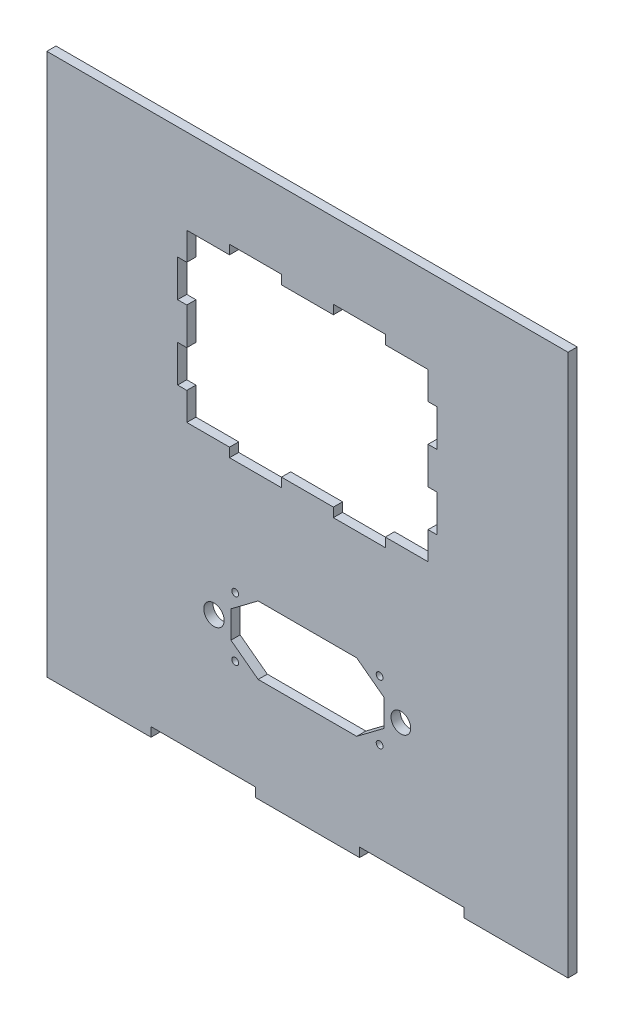
SolidWorks part; units mm, degrees
ref_plane "Ön Düzlem" through (0, 0, 0) normal (0, 0, 1) x (1, 0, 0)
ref_plane "Üst Düzlem" through (0, 0, 0) normal (0, 1, 0) x (1, 0, 0)
ref_plane "Sağ Düzlem" through (0, 0, 0) normal (1, 0, 0) x (0, 0, -1)
sketch "Sketch1" plane through (0, 0, 0) normal (0, 0, 1) x (1, 0, 0)
  line L21 (-46.02, -28) -> (-46.02, -25.3)
  line L22 (-15.34, -28) -> (-15.34, -25.3)
  line L23 (15.34, -28) -> (15.34, -25.3)
  line L24 (46.02, -28) -> (46.02, -25.3)
  line L26 (-76.7, -23) -> (-76.7, 13)
  line L27 (-76.7, -23) -> (-76.7, -25.3)
  line L28 (76.7, -23) -> (76.7, 13)
  line L30 (76.7, -25.3) -> (76.7, -23)
  line L33 (-46.02, -28) -> (-76.7, -28)
  line L34 (-76.7, -28) -> (-76.7, -25.3)
  line L35 (-15.34, -25.3) -> (-46.02, -25.3)
  line L36 (-15.34, -28) -> (15.34, -28)
  line L37 (15.34, -25.3) -> (46.02, -25.3)
  line L38 (46.02, -28) -> (76.7, -28)
  line L39 (76.7, -28) -> (76.7, -25.3)
  line L56 (-22.5, 16.5) -> (-14.5, 22.5)
  line L57 (-14.5, 22.5) -> (14.5, 22.5)
  line L58 (0, 2.5) -> (14.5, 2.5)
  line L59 (-14.5, 2.5) -> (-22.5, 8.5)
  line L60 (-22.5, 8.5) -> (-22.5, 16.5)
  line L61 (14.5, 2.5) -> (22.5, 8.5)
  line L62 (14.5, 22.5) -> (22.5, 16.5)
  line L63 (0, 2.5) -> (-14.5, 2.5)
  line L64 (22.5, 16.5) -> (22.5, 8.5)
  line L65 (35.5, 57.5) -> (22.92, 57.5)
  line L66 (35.5, 57.5) -> (35.5, 65.68)
  line L67 (35.5, 106.5) -> (22.92, 106.5)
  line L68 (-35.5, 57.5) -> (-35.5, 65.68)
  line L80 (76.7, 13) -> (76.7, 131.5)
  line L81 (-76.7, 131.5) -> (-76.7, 13)
  line L82 (76.7, 131.5) -> (-76.7, 131.5)
  line L84 (-22.92, 54.8) -> (-7.64, 54.8)
  line L85 (-22.92, 109.2) -> (-7.64, 109.2)
  line L88 (38.2, 65.68) -> (38.2, 76.56)
  line L89 (7.64, 109.2) -> (22.92, 109.2)
  line L91 (-38.2, 65.68) -> (-38.2, 76.56)
  line L93 (-38.2, 87.44) -> (-38.2, 98.32)
  line L95 (-38.2, 98.32) -> (-35.5, 98.32)
  line L96 (-38.2, 87.44) -> (-35.5, 87.44)
  line L97 (-38.2, 76.56) -> (-35.5, 76.56)
  line L98 (-38.2, 65.68) -> (-35.5, 65.68)
  line L99 (35.5, 65.68) -> (38.2, 65.68)
  line L100 (35.5, 76.56) -> (38.2, 76.56)
  line L101 (35.5, 87.44) -> (38.2, 87.44)
  line L102 (35.5, 98.32) -> (38.2, 98.32)
  line L103 (-22.92, 109.2) -> (-22.92, 106.5)
  line L104 (-7.64, 109.2) -> (-7.64, 106.5)
  line L105 (7.64, 109.2) -> (7.64, 106.5)
  line L106 (22.92, 109.2) -> (22.92, 106.5)
  line L107 (-22.92, 57.5) -> (-22.92, 54.8)
  line L108 (-7.64, 57.5) -> (-7.64, 54.8)
  line L109 (7.64, 57.5) -> (7.64, 54.8)
  line L110 (22.92, 57.5) -> (22.92, 54.8)
  line L111 (-22.92, 106.5) -> (-35.5, 106.5)
  line L112 (7.64, 106.5) -> (-7.64, 106.5)
  line L113 (35.5, 98.32) -> (35.5, 106.5)
  line L114 (35.5, 76.56) -> (35.5, 87.44)
  line L115 (7.64, 57.5) -> (-7.64, 57.5)
  line L116 (-22.92, 57.5) -> (-35.5, 57.5)
  line L117 (-35.5, 76.56) -> (-35.5, 87.44)
  line L118 (-35.5, 98.32) -> (-35.5, 106.5)
  line L119 (38.2, 87.44) -> (38.2, 98.32)
  line L120 (7.64, 54.8) -> (22.92, 54.8)
  circle A11 centre (-21.25, 3.75) radius 1
  circle A12 centre (-27.5, 12.5) radius 3
  circle A13 centre (-21.25, 21.25) radius 1
  circle A14 centre (21.25, 3.75) radius 1
  circle A15 centre (27.5, 12.5) radius 2.9
  circle A16 centre (21.25, 21.25) radius 1
  point P0 (0, 82)
extrude "Boss-Extrude3" add sketch "Sketch1" along normal blind 2.7
